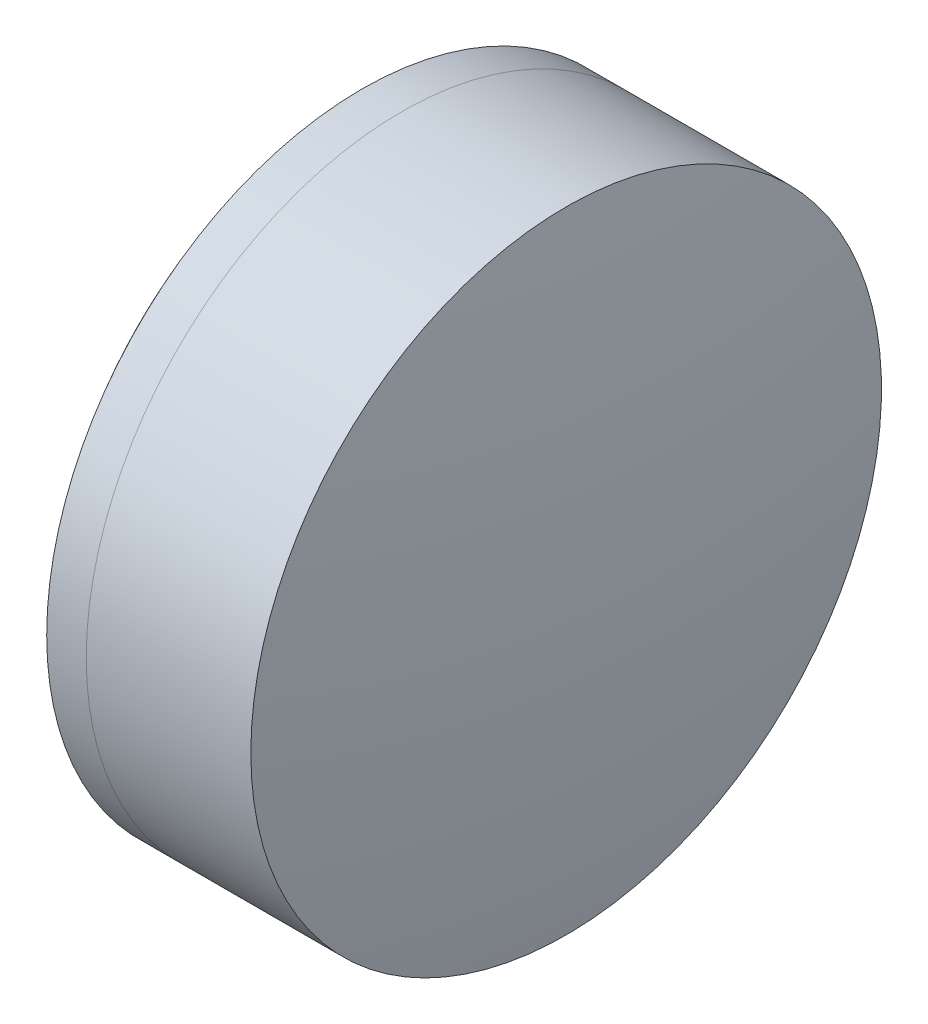
SolidWorks part; units mm, degrees
ref_plane "前视基准面" through (0, 0, 0) normal (0, 0, 1) x (1, 0, 0)
ref_plane "上视基准面" through (0, 0, 0) normal (0, 1, 0) x (1, 0, 0)
ref_plane "右视基准面" through (0, 0, 0) normal (1, 0, 0) x (0, 0, -1)
sketch "草图1" plane through (0, 0, 0) normal (0, 1, 0) x (1, 0, 0)
  line L0 (124.5233, 0) -> (646.9917, 0) construction
  line L1 (272.9116, -12.7) -> (274.5041, -12.7)
  line L2 (272.9116, 12.7) -> (274.5041, 12.7)
  arc A0 (274.5041, -12.7) -> (274.5041, 12.7) centre (264.479, 0) ccw
  arc A1 (272.9116, 12.7) -> (272.9116, -12.7) centre (289.749, 0) ccw
  point P10 (268.659, 0)
  point P11 (280.659, 0)
  dimension "D3" = 21.09
  dimension "D4" = 16.18
  dimension "D1" = 12.7
  dimension "D2" = 12.7
  dimension "D5" = 12
revolve "旋转1" add sketch "草图1" angle 360 about L0
sketch "草图2" plane through (0, 0, 0) normal (0, 1, 0) x (1, 0, 0)
  line L0 (-0.5519, 0) -> (622.6607, 0) construction
  line L2 (274.5041, 12.7) -> (281.1325, 12.7)
  line L3 (274.5041, -12.7) -> (281.1325, -12.7)
  arc A0 (281.1325, -12.7) -> (281.1325, 12.7) centre (203.079, 0) ccw
  arc A1 (274.5041, -12.7) -> (274.5041, 12.7) centre (264.479, 0) ccw construction
  arc A2 (274.5041, -12.7) -> (274.5041, 12.7) centre (264.479, 0) ccw
  point P4 (280.659, 0)
  point P8 (282.159, 0)
  dimension "D1" = 79.08
  dimension "D2" = 1.5
revolve "旋转3" add sketch "草图2" angle 360 about L0
